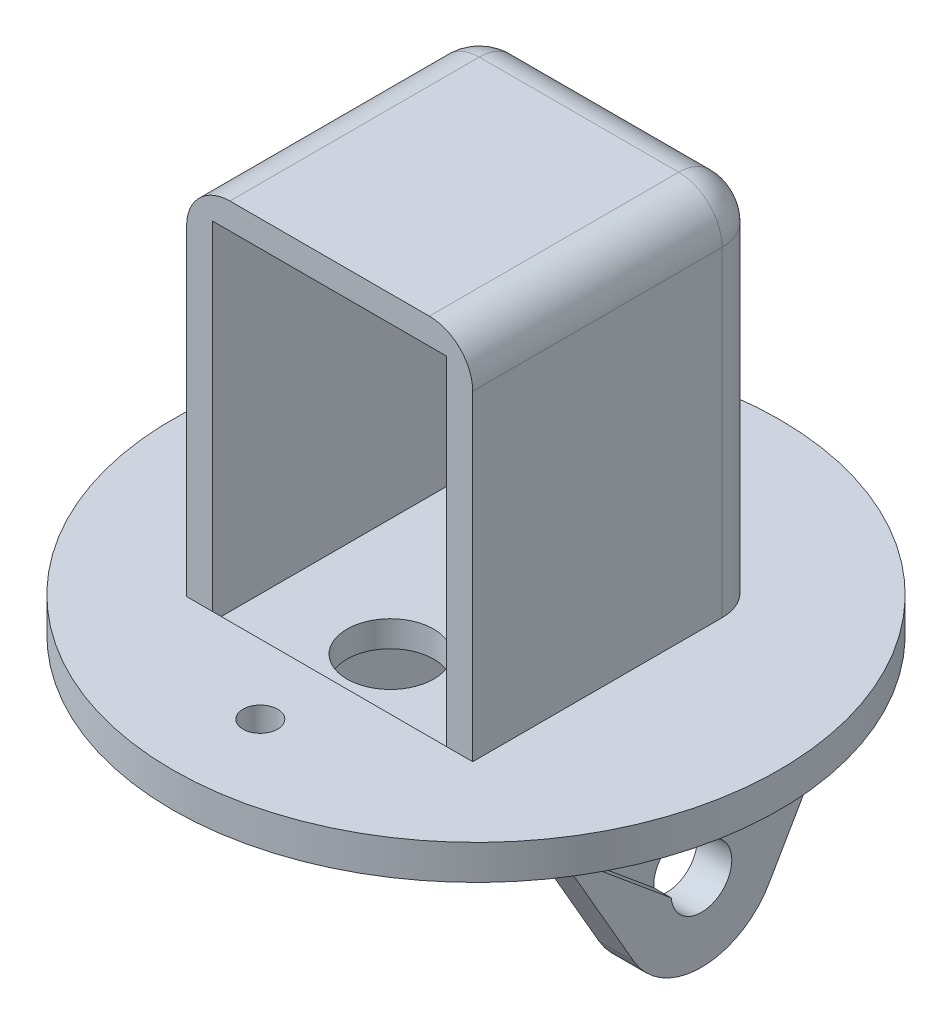
SolidWorks part; units mm, degrees
ref_plane "前视基准面" through (0, 0, 0) normal (0, 0, 1) x (1, 0, 0)
ref_plane "上视基准面" through (0, 0, 0) normal (0, 1, 0) x (1, 0, 0)
ref_plane "右视基准面" through (0, 0, 0) normal (1, 0, 0) x (0, 0, -1)
sketch "草图1" plane through (0, 0, 0) normal (1, 0, 0) x (0, 0, -1)
  circle A0 centre (0, 0) radius 2.5
  circle A1 centre (0, 0) radius 9
  dimension "D1" = 18
  dimension "D2" = 5
extrude "凸台-拉伸1" add sketch "草图1" against normal blind 4
sketch "草图2" plane through (0, 0, 0) normal (1, 0, 0) x (0, 0, -1)
  line L0 (-7.7942, -4.5) -> (-16.8788, 11.2349)
  line L1 (-16.8788, 11.2349) -> (16.876, 11.2349)
  line L2 (16.876, 11.2349) -> (7.8956, -4.3196)
  circle A1 centre (0, 0) radius 9
  circle A2 centre (0, 0) radius 9
  dimension "D2" = 60
  dimension "D3" = 60
  dimension "D1" = 0
extrude "凸台-拉伸2" add sketch "草图2" against normal blind 4 contours A2 L2 L1 L0
sketch "草图6" plane through (0, 0, 0) normal (1, 0, 0) x (0, 0, -1)
  line L1 (-16.8788, 11.2349) -> (16.876, 11.2349)
  line L2 (-16.8788, 11.2349) -> (-16.8788, 14.2349)
  line L3 (-16.8788, 14.2349) -> (16.876, 14.2349)
  line L4 (16.876, 11.2349) -> (16.876, 14.2349)
  dimension "D1" = 3
extrude "凸台-拉伸5" add sketch "草图6" against normal blind 52
ref_plane "基准面1" through (-35.5, 0, 0) normal (1, 0, 0) x (0, 0, -1)
sketch "草图7" plane through (-35.5, 0, 0) normal (1, 0, 0) x (0, 0, -1)
  line L3 (-16.8788, 11.2349) -> (-7.7942, -4.5)
  line L4 (16.876, 11.2349) -> (-16.8788, 11.2349)
  line L5 (7.8956, -4.3196) -> (16.876, 11.2349)
  line L6 (-16.8788, 11.2349) -> (-7.7942, -4.5)
  line L7 (16.876, 11.2349) -> (-16.8788, 11.2349)
  line L8 (7.8956, -4.3196) -> (16.876, 11.2349)
  circle A0 centre (0, 0) radius 2.5 construction
  arc A1 (-7.7942, -4.5) -> (7.8956, -4.3196) centre (0, 0) ccw
  arc A2 (-7.7942, -4.5) -> (7.8956, -4.3196) centre (0, 0) ccw
  circle A3 centre (0, 0) radius 2.5
  dimension "D1" = 0
extrude "凸台-拉伸6" add sketch "草图7" against normal blind 4
sketch "草图8" plane through (-35.5, 0, 0) normal (1, 0, 0) x (0, 0, -1)
  circle A1 centre (0, 0) radius 2.5
  circle A2 centre (0, 0) radius 2.5
  dimension "D1" = 0
extrude "凸台-拉伸7" add sketch "草图8" against normal blind 8
sketch "草图9" plane through (0, 14.2349, 0) normal (0, 1, 0) x (1, 0, 0)
  line L0 (-26, -16.8788) -> (-26, 16.876) construction
  line L1 (-52, -16.8788) -> (0, -16.8788) construction
  line L2 (-52, 16.876) -> (0, 16.876) construction
  line L3 (-12.5, 13.876) -> (-39.5, 13.876)
  line L4 (-42.5, 16.876) -> (-9.5, 16.876)
  line L5 (-42.5, 16.876) -> (-42.5, -16.8788)
  line L6 (-42.5, -16.8788) -> (-9.5, -16.8788)
  line L7 (-9.5, 16.876) -> (-9.5, -16.8788)
  line L8 (-26, -16.8788) -> (-26, 16.876) construction
  line L9 (-42.5, -0.0014) -> (-9.5, -0.0014) construction
  line L10 (-39.5, 16.876) -> (-12.5, 16.876)
  line L11 (-39.5, 16.876) -> (-39.5, -16.8788)
  line L12 (-39.5, -16.8788) -> (-12.5, -16.8788)
  line L13 (-12.5, 16.876) -> (-12.5, -16.8788)
  line L14 (-26, -16.8788) -> (-26, 16.876) construction
  line L15 (-39.5, -0.0014) -> (-12.5, -0.0014) construction
  point P6 (-26, -0.0014)
  point P10 (-26, -0.0014)
  line M7 (0, 16.876) -> (-52, 16.876)
  line M9 (-52, -16.8788) -> (0, -16.8788)
  dimension "D1" = 3
  dimension "D2" = 27
  dimension "D3" = 3
extrude "凸台-拉伸8" add sketch "草图9" along normal blind 40 contours L13 L7 M7 M9 | L11 L5 M7 M9 | L13 L4 L11 L3
sketch "草图10" plane through (0, 0, -13.876) normal (0, 0, 1) x (1, 0, 0)
  line L0 (-26, 54.2349) -> (-26, 14.2349) construction
  line L2 (-22, 50.2349) -> (-30, 50.2349)
  line L3 (-22, 50.2349) -> (-22, 42.2349)
  line L12 (-22, 42.2349) -> (-30, 42.2349)
  line L13 (-30, 50.2349) -> (-30, 42.2349)
  line L14 (-26, 42.2349) -> (-26, 50.2349) construction
  line L15 (-22, 46.2349) -> (-30, 46.2349) construction
  point P6 (-26, 46.2349)
  dimension "D3" = 8
  dimension "D4" = 8
extrude "切除-拉伸1" cut sketch "草图10" against normal blind 40
sketch "草图11" plane through (0, 54.2349, 0) normal (0, 1, 0) x (1, 0, 0)
  line L4 (-12.5, -16.8788) -> (-12.5, 13.876)
  line L5 (-12.5, 13.876) -> (-39.5, 13.876)
  line L6 (-39.5, 13.876) -> (-39.5, -16.8788)
  line L7 (-39.5, -16.8788) -> (-12.5, -16.8788)
  line L8 (-12.5, -16.8788) -> (-12.5, 13.876)
  line L9 (-12.5, 13.876) -> (-39.5, 13.876)
  line L10 (-39.5, 13.876) -> (-39.5, -16.8788)
  line L11 (-39.5, -16.8788) -> (-12.5, -16.8788)
  line L16 (-9.5, 16.876) -> (-42.5, 16.876)
  line L17 (-42.5, 16.876) -> (-42.5, -16.8788)
  line L18 (-42.5, -16.8788) -> (-39.5, -16.8788)
  line L19 (-39.5, -16.8788) -> (-39.5, 13.876)
  line L20 (-39.5, 13.876) -> (-12.5, 13.876)
  line L21 (-12.5, 13.876) -> (-12.5, -16.8788)
  line L22 (-12.5, -16.8788) -> (-9.5, -16.8788)
  line L23 (-9.5, -16.8788) -> (-9.5, 16.876)
  line L24 (-9.5, 16.876) -> (-42.5, 16.876)
  line L25 (-42.5, 16.876) -> (-42.5, -16.8788)
  line L26 (-42.5, -16.8788) -> (-39.5, -16.8788)
  line L27 (-39.5, -16.8788) -> (-39.5, 13.876)
  line L28 (-39.5, 13.876) -> (-12.5, 13.876)
  line L29 (-12.5, 13.876) -> (-12.5, -16.8788)
  line L30 (-12.5, -16.8788) -> (-9.5, -16.8788)
  line L31 (-9.5, -16.8788) -> (-9.5, 16.876)
  line M13 (-9.5, 16.876) -> (-42.5, 16.876)
  line M14 (-42.5, 16.876) -> (-42.5, -16.8788)
  line M15 (-42.5, -16.8788) -> (-39.5, -16.8788)
  line M16 (-39.5, -16.8788) -> (-39.5, 13.876)
  line M17 (-39.5, 13.876) -> (-12.5, 13.876)
  line M18 (-12.5, 13.876) -> (-12.5, -16.8788)
  line M19 (-12.5, -16.8788) -> (-9.5, -16.8788)
  line M20 (-9.5, -16.8788) -> (-9.5, 16.876)
  dimension "D1" = 0
  dimension "D2" = 0
extrude "凸台-拉伸9" add sketch "草图11" along normal blind 3 contours M20 M13 M14 M15 M16 M17 M18 M19 | L11 M16 M18 M17
sketch "草图12" plane through (0, 11.2349, 0) normal (0, -1, 0) x (1, 0, 0)
  line L0 (-26, 16.8788) -> (-26, -16.876) construction
  line L1 (-9.5, 0.0014) -> (-42.5, 0.0014) construction
  line L4 (-9.5, -16.876) -> (-9.5, 16.8788)
  line L5 (-42.5, -16.876) -> (-9.5, -16.876)
  line L6 (-42.5, 16.8788) -> (-42.5, -16.876)
  line L7 (-9.5, 16.8788) -> (-42.5, 16.8788)
  line L8 (-9.5, -16.876) -> (-9.5, 16.8788)
  line L9 (-42.5, -16.876) -> (-9.5, -16.876)
  line L10 (-42.5, 16.8788) -> (-42.5, -16.876)
  line L11 (-9.5, 16.8788) -> (-42.5, 16.8788)
  circle A0 centre (-26, 0.0014) radius 35
  point P2 (-26, 16.8788)
  dimension "D2" = 70
  dimension "D1" = 0
extrude "凸台-拉伸10" add sketch "草图12" against normal blind 4
sketch "草图13" plane through (0, 15.2349, 0) normal (0, 1, 0) x (1, 0, 0)
  line L4 (-12.5, -16.8788) -> (-12.5, 13.876)
  line L5 (-12.5, 13.876) -> (-39.5, 13.876)
  line L6 (-39.5, 13.876) -> (-39.5, -16.8788)
  line L7 (-39.5, -16.8788) -> (-12.5, -16.8788)
  line L11 (-39.5, -16.8788) -> (-12.5, -16.8788)
  circle A0 centre (-26, -24.8788) radius 2
  dimension "D2" = 8
  dimension "D3" = 4
  dimension "D1" = 0
extrude "切除-拉伸2" cut sketch "草图13" against normal blind 4 contours A0
fillet "圆角1" radius 5 5 edges at (-9.5, 36.2349, -16.876) (-42.5, 36.2349, -16.876) (-26, 57.2349, -16.876) (-9.5, 57.2349, 0.0014) (-42.5, 57.2349, 0.0014)
sketch "草图14" plane through (0, 14.2349, 0) normal (0, 1, 0) x (1, 0, 0)
  circle A0 centre (-26, -9.8788) radius 5
  dimension "D2" = 10
extrude "切除-拉伸3" cut sketch "草图14" against normal blind 3
sketch "草图15" plane through (0, 0, 0) normal (1, 0, 0) x (0, 0, -1)
  line L0 (0, 0) -> (-11.653, 8.6289)
  line L1 (-12.7086, 7.3597) -> (-1.3894, -2.0545)
  line L2 (-10.7501, 10.0108) -> (1.1704, 2.2216)
  circle A0 centre (0, 0) radius 3.5
  circle A1 centre (-11.653, 8.6289) radius 1.6507
  circle A2 centre (0, 0) radius 2.5 construction
  circle A3 centre (0, 0) radius 2.5
  point P9 (-2.5, -2.5)
  point P10 (0, 0)
  point P11 (-1.6144, -2.325)
  point P12 (1.3629, 2.5162)
  dimension "D1" = 7
  dimension "D2" = 14.5
extrude "切除-拉伸4" cut sketch "草图15" against normal blind 2
sketch "草图16" plane through (0, 0, 0) normal (1, 0, 0) x (0, 0, -1)
  circle A0 centre (0, 0) radius 3.5
extrude "切除-拉伸5" cut sketch "草图16" against normal blind 6
